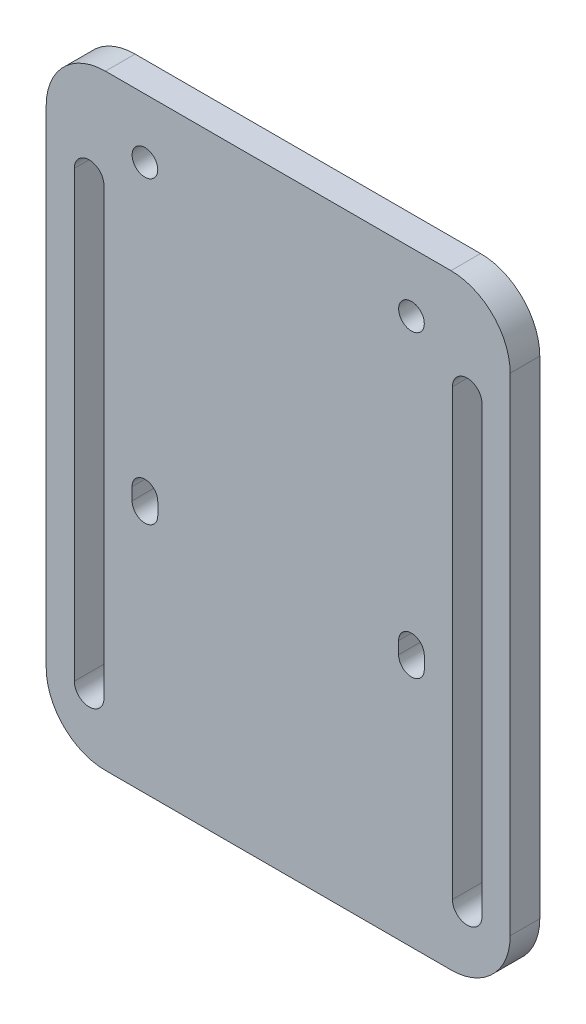
SolidWorks part; units mm, degrees
material "Polycarbonate (PC)"
ref_plane "Спереди" through (0, 0, 0) normal (0, 0, 1) x (1, 0, 0)
ref_plane "Сверху" through (0, 0, 0) normal (0, 1, 0) x (1, 0, 0)
ref_plane "Справа" through (0, 0, 0) normal (1, 0, 0) x (0, 0, -1)
sketch "Model" plane through (0, 0, 0) normal (0, 0, 1) x (1, 0, 0)
  line L0 (0, 130.393) -> (0, -19.607) construction
  line L1 (38.3, 119.0065) -> (38.3, 3.8567) construction
  line L2 (39.6393, 110.7) -> (20.3566, 110.7) construction
  line L3 (27, 114.3973) -> (27, 106.7903) construction
  line L8 (27, 57.0366) -> (27, 46.0463) construction
  line L14 (-27, 114.3973) -> (-27, 106.7903) construction
  line L15 (-39.6393, 110.7) -> (-20.3566, 110.7) construction
  line L16 (-29.6, 50) -> (-29.6, 52.5)
  line L17 (-29.6, 52.5) -> (-29.6, 50)
  line L18 (-27, 57.0366) -> (-27, 46.0463) construction
  line L19 (-24.4, 52.5) -> (-24.4, 50)
  line L20 (-24.4, 50) -> (-24.4, 52.5)
  line L22 (-41.3, 12.5) -> (-41.3, 102.5)
  line L23 (-41.3, 102.5) -> (-41.3, 12.5)
  line L24 (-38.3, 119.0065) -> (-38.3, 3.8567) construction
  line L25 (-35.3, 102.5) -> (-35.3, 12.5)
  line L26 (-35.3, 12.5) -> (-35.3, 102.5)
  line L29 (-41.3, 12.5) -> (-35.3, 12.5) construction
  line L2974 (29.6, 52.5) -> (29.6, 50)
  line L2987 (24.4, 50) -> (24.4, 52.5)
  line L2994 (35.3, 12.5) -> (35.3, 102.5)
  line L3007 (41.3, 102.5) -> (41.3, 12.5)
  line L3504 (35, 0) -> (-35, 0)
  line L3511 (-47, 12) -> (-47, 110.7)
  line L3518 (-35, 122.7) -> (35, 122.7)
  line L3525 (47, 110.7) -> (47, 12)
  line L3777 (24.4, 52.5) -> (24.4, 50)
  line L3790 (29.6, 50) -> (29.6, 52.5)
  line L3887 (41.3, 12.5) -> (41.3, 102.5)
  line L3900 (35.3, 102.5) -> (35.3, 12.5)
  arc A0 (-47, 12) -> (-35, 0) centre (-35, 12) ccw
  arc A1 (35, 0) -> (47, 12) centre (35, 12) ccw
  arc A2 (47, 110.7) -> (35, 122.7) centre (35, 110.7) ccw
  arc A3 (-47, 110.7) -> (-35, 122.7) centre (-35, 110.7) cw
  circle A8 centre (27, 110.7) radius 2.6
  arc A9 (24.4, 52.5) -> (29.6, 52.5) centre (27, 52.5) cw
  arc A10 (24.4, 50) -> (29.6, 50) centre (27, 50) ccw
  arc A11 (35.3, 12.5) -> (41.3, 12.5) centre (38.3, 12.5) ccw
  arc A12 (35.3, 102.5) -> (41.3, 102.5) centre (38.3, 102.5) cw
  arc A17 (-35.3, 102.5) -> (-41.3, 102.5) centre (-38.3, 102.5) ccw
  circle A18 centre (-27, 110.7) radius 2.6
  arc A19 (-24.4, 50) -> (-29.6, 50) centre (-27, 50) cw
  arc A20 (-24.4, 52.5) -> (-29.6, 52.5) centre (-27, 52.5) ccw
  arc A22 (-35.3, 12.5) -> (-41.3, 12.5) centre (-38.3, 12.5) cw
  dimension "D1" = 12
  dimension "D17" = 5.2
  dimension "D22" = 2.6
  dimension "D23" = 2.6
  dimension "D26" = 90
  dimension "D6" = 54
  dimension "D3" = 122.7
  dimension "D4" = 76.6
  dimension "D5" = 60.7
  dimension "D7" = 54
  dimension "D8" = 94
  dimension "D20" = 2.5
  dimension "D21" = 5.2
  dimension "D24" = 50
  dimension "D25" = 6
  dimension "D27" = 12.5
extrude "Base" add sketch "Model" along normal blind 6
